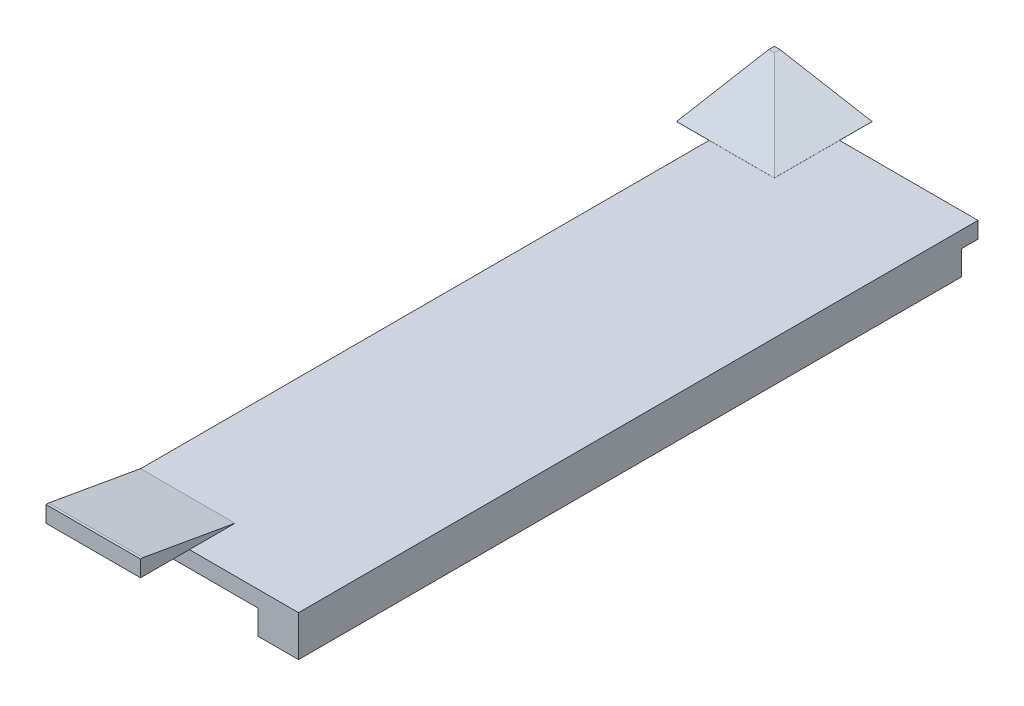
SolidWorks part; units mm, degrees
ref_plane "Front Plane" through (0, 0, 0) normal (0, 0, 1) x (1, 0, 0)
ref_plane "Top Plane" through (0, 0, 0) normal (0, 1, 0) x (1, 0, 0)
ref_plane "Right Plane" through (0, 0, 0) normal (1, 0, 0) x (0, 0, -1)
sketch "Sketch1" plane through (0, 0, 0) normal (0, 1, 0) x (1, 0, 0)
  line L1 (0, 0) -> (25, 0)
  line L2 (0, 0) -> (0, 83.4)
  line L3 (0, 83.4) -> (25, 83.4)
  line L4 (25, 0) -> (25, 83.4)
  dimension "D1" = 83.4
  dimension "D2" = 25
extrude "Boss-Extrude1" add sketch "Sketch1" along normal blind 2
sketch "Sketch2" plane through (0, 2, 0) normal (0, 1, 0) x (1, 0, 0)
  line L0 (0, 83.4) -> (0, 0) construction
  line L1 (0, 5.6) -> (11.6, 5.6)
  line L2 (0, 5.6) -> (0, -6)
  line L3 (0, -6) -> (11.6, -6)
  line L4 (11.6, 5.6) -> (11.6, -6)
  line L5 (25, 83.4) -> (0, 83.4) construction
  line L6 (0, 0) -> (25, 0) construction
  line L7 (8, 75.4) -> (-4, 75.4)
  line L8 (8, 75.4) -> (8, 87.4)
  line L9 (8, 87.4) -> (-4, 87.4)
  line L10 (-4, 75.4) -> (-4, 87.4)
  dimension "D1" = 11.6
  dimension "D2" = 6
  dimension "D3" = 5.6
  dimension "D4" = 8
  dimension "D5" = 8
  dimension "D6" = 4
  dimension "D7" = 4
extrude "Boss-Extrude2" add sketch "Sketch2" along normal blind 2
chamfer "Chamfer1" distance 11.3 angle 10 3 edges at (5.8, 4, -5.6) (8, 4, -81.4) (2, 4, -75.4)
sketch "Sketch4" plane through (0, 0, 0) normal (0, -1, 0) x (1, 0, 0)
  line L0 (25, -83.4) -> (0, -83.4) construction
  line L1 (25, -81.4) -> (20, -81.4)
  line L2 (25, -81.4) -> (25, 0)
  line L3 (25, 0) -> (20, 0)
  line L4 (20, -81.4) -> (20, 0)
  line L5 (25, 0) -> (25, -83.4) construction
  dimension "D1" = 81.4
  dimension "D2" = 5
  dimension "D3" = 2
  dimension "D4" = 0
extrude "Boss-Extrude3" add sketch "Sketch4" along normal blind 3
